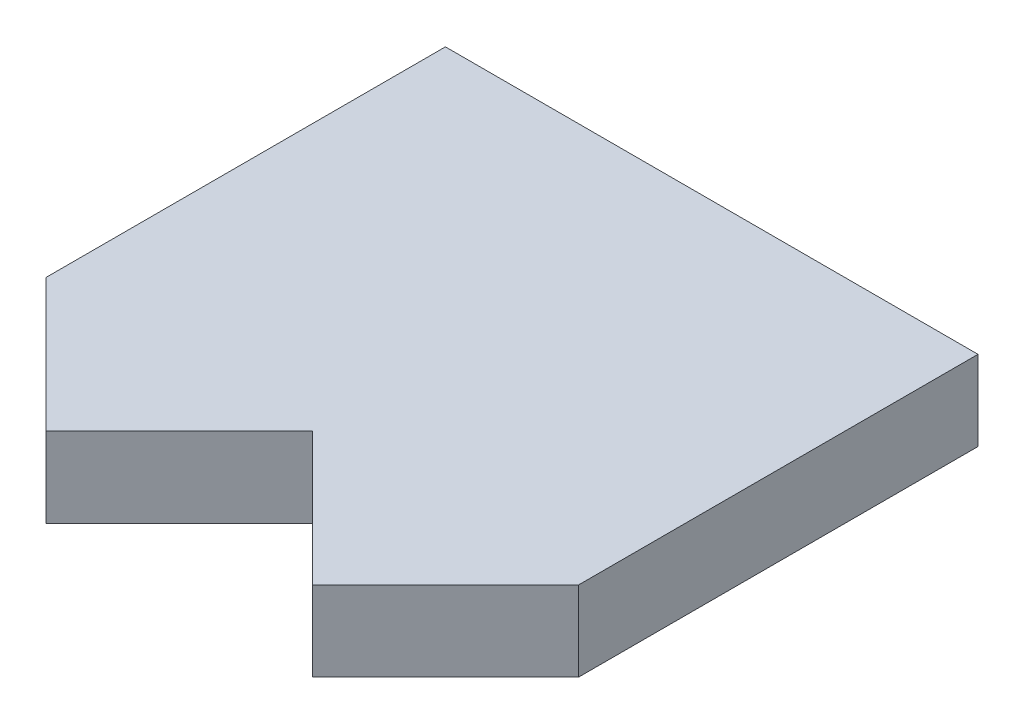
SolidWorks part; units mm, degrees
ref_plane "Front Plane" through (0, 0, 0) normal (0, 0, 1) x (1, 0, 0)
ref_plane "Top Plane" through (0, 0, 0) normal (0, 1, 0) x (1, 0, 0)
ref_plane "Right Plane" through (0, 0, 0) normal (1, 0, 0) x (0, 0, -1)
sketch "Sketch1" plane through (0, 0, 0) normal (0, 1, 0) x (1, 0, 0)
  line L1 (-10, -10) -> (10, -10)
  line L2 (-10, -10) -> (-10, 10)
  line L3 (-10, 10) -> (10, 10)
  line L4 (10, -10) -> (10, 10)
  line L5 (-10, -10) -> (10, 10) construction
  line L6 (-10, 10) -> (10, -10) construction
  point P0 (0, 0)
  dimension "D1" = 20
  dimension "D2" = 20
extrude "Boss-Extrude1" add sketch "Sketch1" along normal blind 3
sketch "Sketch2" plane through (0, 3, 0) normal (0, 1, 0) x (1, 0, 0)
  line L0 (-10, -5) -> (-5, -10)
  line L1 (-10, 10) -> (-10, -10) construction
  line L2 (-10, -10) -> (10, -10) construction
  line L3 (-5, -10) -> (0, -5)
  line L4 (0, -5) -> (5, -10)
  line L5 (5, -10) -> (10, -5)
  line L6 (10, -10) -> (10, 10) construction
  line L7 (10, -5) -> (10, -10)
  line L8 (10, -10) -> (-10, -10)
  line L9 (-10, -10) -> (-10, -5)
  point P6 (0, 0)
  point P17 (0.3387, -3.0239)
  point P18 (-3.7254, -5)
  point P20 (0, -5)
  line M1 (10, -10) -> (10, 10)
  line M3 (-10, 10) -> (-10, -10)
  line M4 (-10, -10) -> (10, -10)
  dimension "D1" = 5
  dimension "D2" = 5
  dimension "D3" = 5
extrude "Cut-Extrude1" cut sketch "Sketch2" against normal through all both and the other way through all contours L0 M3 M4 | L4 L3 M4 | L5 M4 M1
